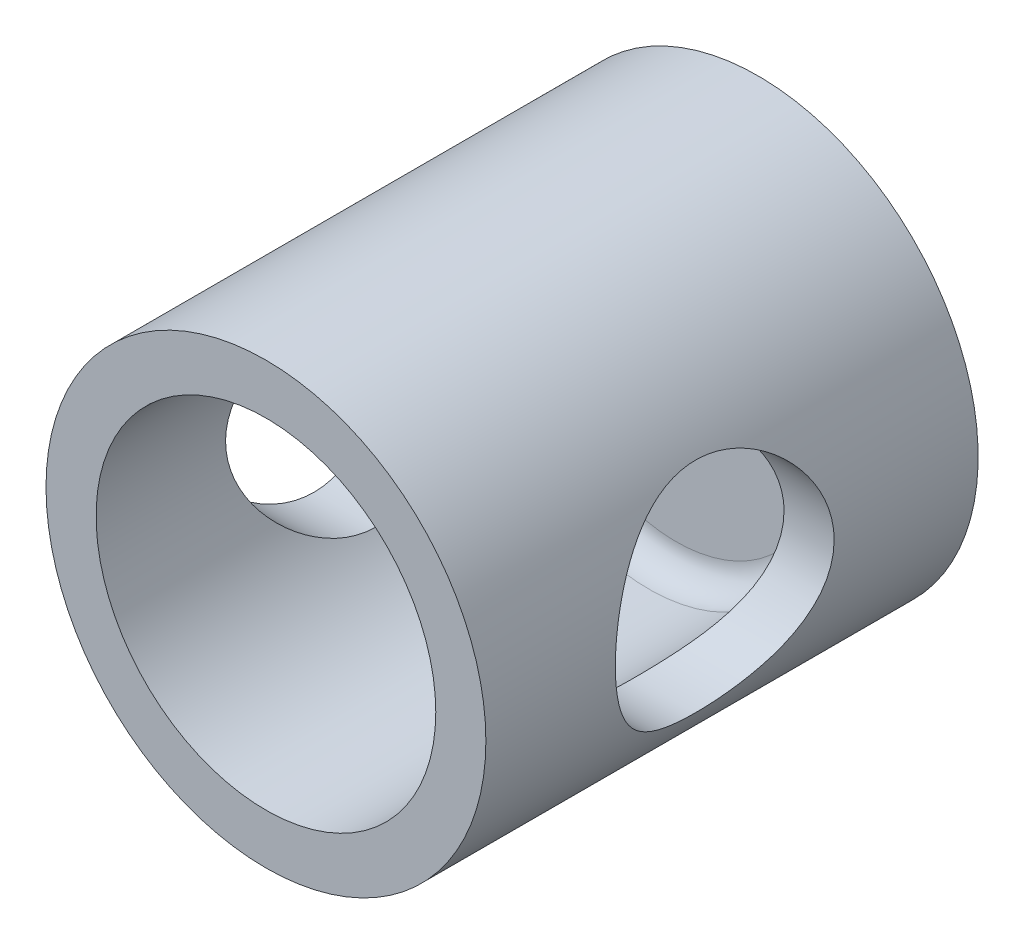
SolidWorks part; units mm, degrees
ref_plane "Front Plane" through (0, 0, 0) normal (0, 0, 1) x (1, 0, 0)
ref_plane "Top Plane" through (0, 0, 0) normal (0, 1, 0) x (1, 0, 0)
ref_plane "Right Plane" through (0, 0, 0) normal (1, 0, 0) x (0, 0, -1)
sketch "Sketch2" plane through (0, 0, 0) normal (0, 0, 1) x (1, 0, 0)
  circle A0 centre (0, 0) radius 10
  dimension "D1" = 20
extrude "Boss-Extrude1" add sketch "Sketch2" along normal blind 18
sketch "Sketch5" plane through (0, 0, 0) normal (1, 0, 0) x (0, 0, -1)
  circle A0 centre (-9.266, 0) radius 4
  dimension "D1" = 8
extrude "Cut-Extrude1" cut sketch "Sketch5" along normal blind 18 and the other way blind 21
sketch "Sketch6" plane through (0, 0, 0) normal (0, 0, -1) x (-1, 0, 0)
  circle A0 centre (0, 0) radius 8.0421
extrude "Cut-Extrude2" cut sketch "Sketch6" against normal blind 24 flip side to cut contours A0
sketch "Sketch8" plane through (0, 0, 18) normal (0, 0, 1) x (1, 0, 0)
  circle A0 centre (0, 0) radius 6.2103
extrude "Cut-Extrude4" cut sketch "Sketch8" against normal blind 15 contours A0
fillet "Fillet1" radius 1 1 edges at (6.2103, 0, 3)
